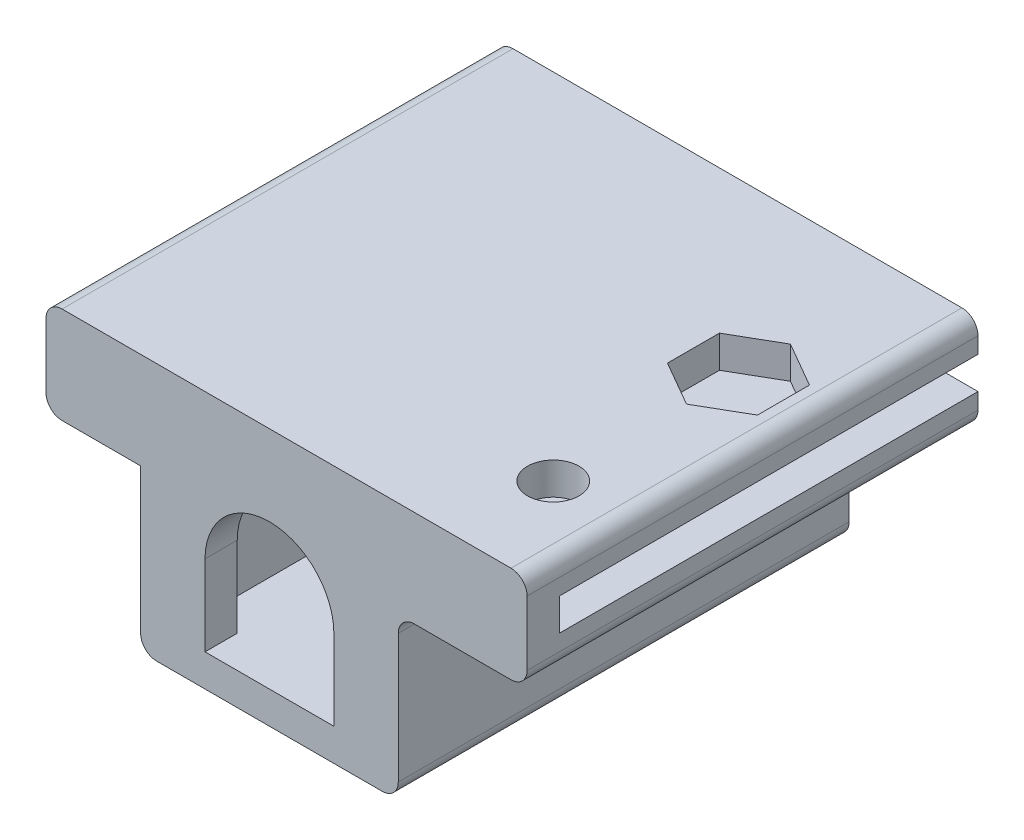
SolidWorks part; units mm, degrees
ref_plane "前视基准面" through (0, 0, 0) normal (0, 0, 1) x (1, 0, 0)
ref_plane "上视基准面" through (0, 0, 0) normal (0, 1, 0) x (1, 0, 0)
ref_plane "右视基准面" through (0, 0, 0) normal (1, 0, 0) x (0, 0, -1)
sketch "草图1" plane through (0, 0, 0) normal (0, 0, 1) x (1, 0, 0)
  line L0 (9, 3) -> (15, 3)
  line L1 (7, -7) -> (-7, -7)
  line L2 (8, -6) -> (8, 2)
  line L3 (8, 5) -> (-8, 5)
  line L4 (6, -4) -> (6, 4)
  line L5 (5, 5) -> (-5, 5)
  line L6 (-6, 4) -> (-6, -4)
  line L7 (-5, -5) -> (5, -5)
  line L8 (6, -4) -> (6, 4)
  line L9 (5, 5) -> (-5, 5)
  line L10 (-6, 4) -> (-6, -4)
  line L11 (-5, -5) -> (5, -5)
  line L12 (88.125, 7) -> (-11.875, 7)
  line L13 (-11.875, 7) -> (-11.875, 5)
  line L14 (-11.875, 5) -> (88.125, 5)
  line L15 (88.125, 5) -> (88.125, 7)
  line L16 (88.125, 7) -> (-11.875, 7)
  line L17 (-11.875, 7) -> (-11.875, 5)
  line L18 (-11.875, 5) -> (88.125, 5)
  line L19 (88.125, 5) -> (88.125, 7)
  line L20 (-8, -6) -> (-8, 3)
  line L21 (-12.875, 3) -> (-8, 3)
  line L22 (-13.875, 4) -> (-13.875, 8)
  line L23 (-12.875, 9) -> (15, 9)
  line L24 (16, 4) -> (16, 8)
  line L26 (4, 0) -> (4, -5)
  line L27 (4, -5) -> (-4, -5)
  line L28 (-4, 0) -> (-4, -5)
  arc A0 (4, 0) -> (-4, 0) centre (0, 0) ccw
  arc A1 (15, 9) -> (16, 8) centre (15, 8) cw
  arc A2 (8, 2) -> (9, 3) centre (9, 2) cw
  arc A3 (16, 4) -> (15, 3) centre (15, 4) cw
  arc A4 (6, 4) -> (5, 5) centre (5, 4) ccw
  arc A5 (-5, 5) -> (-6, 4) centre (-5, 4) ccw
  arc A6 (-6, -4) -> (-5, -5) centre (-5, -4) ccw
  arc A7 (5, -5) -> (6, -4) centre (5, -4) ccw
  arc A8 (6, 4) -> (5, 5) centre (5, 4) ccw
  arc A9 (-5, 5) -> (-6, 4) centre (-5, 4) ccw
  arc A10 (-6, -4) -> (-5, -5) centre (-5, -4) ccw
  arc A11 (5, -5) -> (6, -4) centre (5, -4) ccw
  arc A12 (8, -6) -> (7, -7) centre (7, -6) cw
  arc A13 (-7, -7) -> (-8, -6) centre (-7, -6) cw
  arc A14 (-13.875, 8) -> (-12.875, 9) centre (-12.875, 8) cw
  arc A15 (-12.875, 3) -> (-13.875, 4) centre (-12.875, 4) cw
  dimension "D3" = 1
  dimension "D5" = 2
  dimension "D6" = 2
  dimension "D1" = 0
  dimension "D2" = 0
extrude "凸台-拉伸1" add sketch "草图1" along normal blind 2 contours A11 L11 A10 L10 A9 L3 L18 L17 L16 L24 L23 L22 L21 L20 L1 L2 L0 A8 L8 | L18 L24 L16 L17 L3 | L11 A11 L8 A8 L3 A9 L10 A10 L28 A0 L26
sketch "草图2" plane through (0, 0, 0) normal (0, 0, -1) x (-1, 0, 0)
  line L1 (6, -5) -> (-6, -5)
  line L2 (6, -5) -> (6, 5)
  line L3 (6, 5) -> (-6, 5)
  line L4 (-6, 4) -> (-6, -4)
  line L5 (5, 5) -> (-5, 5)
  line L6 (6, -4) -> (6, 4)
  line L7 (-5, -5) -> (5, -5)
  line L8 (-6, 4) -> (-6, -4)
  line L9 (5, 5) -> (-5, 5)
  line L10 (6, -4) -> (6, 4)
  line L11 (-5, -5) -> (5, -5)
  line L12 (-16, 8) -> (-16, 4)
  line L13 (-15, 3) -> (-9, 3)
  line L14 (-8, 2) -> (-8, -6)
  line L15 (-7, -7) -> (7, -7)
  line L16 (8, -6) -> (8, 3)
  line L17 (8, 3) -> (12.875, 3)
  line L18 (13.875, 4) -> (13.875, 8)
  line L19 (12.875, 9) -> (-15, 9)
  line L23 (11.875, 7) -> (-88.125, 7)
  line L24 (-16, 8) -> (-16, 4)
  line L25 (-15, 3) -> (-9, 3)
  line L26 (-8, 2) -> (-8, -6)
  line L27 (-7, -7) -> (7, -7)
  line L28 (8, -6) -> (8, 3)
  line L29 (8, 3) -> (12.875, 3)
  line L30 (13.875, 4) -> (13.875, 8)
  line L31 (12.875, 9) -> (-15, 9)
  line L36 (-6, -5) -> (-6, 5)
  line L37 (11.875, 5) -> (11.875, 7)
  line L38 (-88.125, 5) -> (11.875, 5)
  line L39 (-88.125, 7) -> (-88.125, 5)
  line L40 (11.875, 7) -> (-88.125, 7)
  line L41 (11.875, 5) -> (11.875, 7)
  line L42 (-88.125, 5) -> (11.875, 5)
  line L43 (-88.125, 7) -> (-88.125, 5)
  arc A4 (-5, 5) -> (-6, 4) centre (-5, 4) ccw
  arc A5 (6, 4) -> (5, 5) centre (5, 4) ccw
  arc A6 (5, -5) -> (6, -4) centre (5, -4) ccw
  arc A7 (-6, -4) -> (-5, -5) centre (-5, -4) ccw
  arc A8 (-5, 5) -> (-6, 4) centre (-5, 4) ccw
  arc A9 (6, 4) -> (5, 5) centre (5, 4) ccw
  arc A10 (5, -5) -> (6, -4) centre (5, -4) ccw
  arc A11 (-6, -4) -> (-5, -5) centre (-5, -4) ccw
  arc A15 (-16, 4) -> (-15, 3) centre (-15, 4) ccw
  arc A16 (-16, 4) -> (-15, 3) centre (-15, 4) ccw
  arc A17 (-8, 2) -> (-9, 3) centre (-9, 2) ccw
  arc A18 (-8, 2) -> (-9, 3) centre (-9, 2) ccw
  arc A19 (-8, -6) -> (-7, -7) centre (-7, -6) ccw
  arc A20 (-8, -6) -> (-7, -7) centre (-7, -6) ccw
  arc A21 (7, -7) -> (8, -6) centre (7, -6) ccw
  arc A22 (7, -7) -> (8, -6) centre (7, -6) ccw
  arc A23 (12.875, 3) -> (13.875, 4) centre (12.875, 4) ccw
  arc A24 (12.875, 3) -> (13.875, 4) centre (12.875, 4) ccw
  arc A25 (13.875, 8) -> (12.875, 9) centre (12.875, 8) ccw
  arc A26 (13.875, 8) -> (12.875, 9) centre (12.875, 8) ccw
  arc A27 (-15, 9) -> (-16, 8) centre (-15, 8) ccw
  arc A28 (-15, 9) -> (-16, 8) centre (-15, 8) ccw
  dimension "D1" = 0
  dimension "D2" = 0
  dimension "D3" = 0
extrude "凸台-拉伸2" add sketch "草图2" along normal offset from surface (26 mm away) 2
sketch "草图3" plane through (0, 0, -26) normal (0, 0, -1) x (-1, 0, 0)
  line L1 (6, -5) -> (-6, -5)
  line L2 (6, -5) -> (6, -4)
  line L3 (6, -4) -> (-6, -4)
  line L4 (-6, -5) -> (-6, -4)
  line L20 (-16, 5) -> (-16, 4)
  line L21 (-15, 3) -> (-9, 3)
  line L22 (-8, 2) -> (-8, -6)
  line L23 (-7, -7) -> (7, -7)
  line L24 (8, -6) -> (8, 3)
  line L25 (8, 3) -> (12.875, 3)
  line L26 (13.875, 4) -> (13.875, 8)
  line L27 (12.875, 9) -> (-15, 9)
  line L28 (6, 5) -> (6, -5)
  line L29 (6, 5) -> (6, -5)
  line L30 (6, -5) -> (-6, -5)
  line L31 (6, -5) -> (-6, -5)
  line L37 (-15, 3) -> (-9, 3)
  line L38 (-8, 2) -> (-8, -6)
  line L39 (-7, -7) -> (7, -7)
  line L40 (8, -6) -> (8, 3)
  line L41 (8, 3) -> (12.875, 3)
  line L42 (13.875, 4) -> (13.875, 8)
  line L43 (12.875, 9) -> (-15, 9)
  line L48 (-6, -5) -> (-6, 5)
  line L49 (-6, -5) -> (-6, 5)
  line L50 (-6, 5) -> (-16, 5)
  line L51 (-6, 5) -> (-16, 5)
  line L52 (-16, 8) -> (-16, 7)
  line L53 (-16, 8) -> (-16, 7)
  line L54 (-16, 7) -> (11.875, 7)
  line L55 (-16, 7) -> (11.875, 7)
  line L56 (11.875, 7) -> (11.875, 5)
  line L57 (11.875, 7) -> (11.875, 5)
  line L58 (11.875, 5) -> (6, 5)
  line L59 (11.875, 5) -> (6, 5)
  line L60 (-16, 5) -> (-16, 4)
  arc A7 (-16, 4) -> (-15, 3) centre (-15, 4) ccw
  arc A8 (-16, 4) -> (-15, 3) centre (-15, 4) ccw
  arc A9 (-8, 2) -> (-9, 3) centre (-9, 2) ccw
  arc A10 (-8, 2) -> (-9, 3) centre (-9, 2) ccw
  arc A11 (-8, -6) -> (-7, -7) centre (-7, -6) ccw
  arc A12 (-8, -6) -> (-7, -7) centre (-7, -6) ccw
  arc A13 (7, -7) -> (8, -6) centre (7, -6) ccw
  arc A14 (7, -7) -> (8, -6) centre (7, -6) ccw
  arc A15 (12.875, 3) -> (13.875, 4) centre (12.875, 4) ccw
  arc A16 (12.875, 3) -> (13.875, 4) centre (12.875, 4) ccw
  arc A17 (13.875, 8) -> (12.875, 9) centre (12.875, 8) ccw
  arc A18 (13.875, 8) -> (12.875, 9) centre (12.875, 8) ccw
  arc A19 (-15, 9) -> (-16, 8) centre (-15, 8) ccw
  arc A20 (-15, 9) -> (-16, 8) centre (-15, 8) ccw
  line M19 (6, 5) -> (6, -5)
  line M20 (6, -5) -> (-6, -5)
  line M21 (-6, -5) -> (-6, 5)
  dimension "D2" = 1
  dimension "D1" = 0
extrude "凸台-拉伸3" add sketch "草图3" against normal blind 1.6 contours L3 M19 M21 M20
sketch "草图4" plane through (0, 9, 0) normal (0, 1, 0) x (1, 0, 0)
  line L0 (13.92, 16.825) -> (9.33, 14.175) construction
  line L2 (11.625, 12.2726) -> (14.42, 13.8863)
  line L3 (14.42, 13.8863) -> (14.42, 17.1137)
  line L4 (15, -2) -> (15, 26)
  line L5 (15, 26) -> (-12.875, 26)
  line L6 (15, -2) -> (15, 26)
  line L7 (-12.875, -2) -> (15, -2)
  line L9 (15, 26) -> (-12.875, 26)
  line L11 (-12.875, -2) -> (15, -2)
  line L12 (14.42, 17.1137) -> (11.625, 18.7274)
  line L13 (11.625, 18.7274) -> (8.83, 17.1137)
  line L14 (11.625, 18.15) -> (9.33, 16.825)
  line L15 (9.33, 16.825) -> (9.33, 14.175)
  line L16 (9.33, 14.175) -> (11.625, 12.85)
  line L17 (11.625, 12.85) -> (13.92, 14.175)
  line L18 (13.92, 14.175) -> (13.92, 16.825)
  line L19 (13.92, 16.825) -> (11.625, 18.15)
  line L20 (11.625, 18.15) -> (9.33, 16.825)
  line L21 (9.33, 16.825) -> (9.33, 14.175)
  line L22 (9.33, 14.175) -> (11.625, 12.85)
  line L23 (11.625, 12.85) -> (13.92, 14.175)
  line L24 (13.92, 14.175) -> (13.92, 16.825)
  line L25 (13.92, 16.825) -> (11.625, 18.15)
  line L26 (8.83, 17.1137) -> (8.83, 13.8863)
  line L27 (8.83, 13.8863) -> (11.625, 12.2726)
  line L31 (-12.875, 26) -> (-12.875, -2)
  line L32 (-12.875, 26) -> (-12.875, -2)
  circle A0 centre (11.625, 15.5) radius 2.795 construction
  dimension "D3" = 0.5
  dimension "D1" = 0
  dimension "D2" = 0
extrude "切除-拉伸1" cut sketch "草图4" against normal blind 2 contours L2 L3 L12 L13 L26 L27
sketch "草图5" plane through (0, 3, 0) normal (0, -1, 0) x (1, 0, 0)
  line L0 (11.625, -18.6754) -> (11.625, 2) construction
  line L1 (11.625, -18.6754) -> (14.375, -17.0877)
  line L2 (14.375, -17.0877) -> (14.375, -13.9123)
  line L3 (14.375, -13.9123) -> (11.625, -12.3246)
  line L4 (9, 2) -> (9, -26)
  line L5 (9, -26) -> (15, -26)
  line L6 (9, 2) -> (9, -26)
  line L7 (15, 2) -> (9, 2)
  line L9 (9, -26) -> (15, -26)
  line L11 (15, 2) -> (9, 2)
  line L12 (11.625, -12.3246) -> (8.875, -13.9123)
  line L13 (8.875, -13.9123) -> (8.875, -17.0877)
  line L14 (8.875, -17.0877) -> (11.625, -18.6754)
  line L19 (15, -26) -> (15, 2)
  line L20 (15, -26) -> (15, 2)
  circle A0 centre (11.625, -15.5) radius 1.25 construction
  circle A1 centre (11.625, -15.5) radius 1.25
  circle A2 centre (11.625, -15.5) radius 2.75 construction
  dimension "D2" = 5.5
  dimension "D1" = 0
extrude "切除-拉伸2" cut sketch "草图5" against normal blind 0.5 and the other way through all contours L12 L13 L14 L1 L2 L3
sketch "草图6" plane through (0, 3, 0) normal (0, -1, 0) x (1, 0, 0)
  line L0 (11.625, -18.6754) -> (11.625, 2) construction
  line L1 (14.375, -17.0877) -> (8.875, -13.9123) construction
  line L2 (8.625, -5.7321) -> (11.625, -7.4641)
  line L3 (11.625, -7.4641) -> (14.625, -5.7321)
  line L4 (14.375, -17.0877) -> (11.625, -18.6754)
  line L5 (9, -26) -> (15, -26)
  line L6 (14.375, -17.0877) -> (11.625, -18.6754)
  line L7 (15, 2) -> (9, 2)
  line L9 (9, -26) -> (15, -26)
  line L11 (15, 2) -> (9, 2)
  line L12 (14.625, -5.7321) -> (14.625, -2.2679)
  line L13 (14.625, -2.2679) -> (11.625, -0.5359)
  line L14 (14.375, -13.9123) -> (11.625, -12.3246)
  line L15 (11.625, -12.3246) -> (8.875, -13.9123)
  line L16 (8.875, -13.9123) -> (8.875, -17.0877)
  line L17 (8.875, -17.0877) -> (11.625, -18.6754)
  line L18 (11.625, -18.6754) -> (14.375, -17.0877)
  line L19 (14.375, -17.0877) -> (14.375, -13.9123)
  line L20 (14.375, -13.9123) -> (11.625, -12.3246)
  line L21 (11.625, -12.3246) -> (8.875, -13.9123)
  line L22 (8.875, -13.9123) -> (8.875, -17.0877)
  line L23 (8.875, -17.0877) -> (11.625, -18.6754)
  line L24 (11.625, -18.6754) -> (14.375, -17.0877)
  line L25 (14.375, -17.0877) -> (14.375, -13.9123)
  line L26 (11.625, -0.5359) -> (8.625, -2.2679)
  line L27 (8.625, -2.2679) -> (8.625, -5.7321)
  line L38 (11.625, -18.6754) -> (9, -17.1599)
  line L39 (11.625, -18.6754) -> (9, -17.1599)
  line L40 (9, -17.1599) -> (9, -26)
  line L41 (9, -17.1599) -> (9, -26)
  line L42 (15, -26) -> (15, 2)
  line L43 (15, -26) -> (15, 2)
  line L44 (9, 2) -> (9, -13.8401)
  line L45 (9, 2) -> (9, -13.8401)
  line L46 (9, -13.8401) -> (11.625, -12.3246)
  line L47 (9, -13.8401) -> (11.625, -12.3246)
  line L48 (11.625, -12.3246) -> (14.375, -13.9123)
  line L49 (11.625, -12.3246) -> (14.375, -13.9123)
  line L50 (14.375, -13.9123) -> (14.375, -17.0877)
  line L51 (14.375, -13.9123) -> (14.375, -17.0877)
  circle A0 centre (11.625, -4) radius 3 construction
  point P6 (11.625, -15.5)
  dimension "D3" = 6
  dimension "D4" = 11.5
  dimension "D1" = 0
  dimension "D2" = 0
extrude "切除-拉伸3" cut sketch "草图6" against normal blind 1 and the other way through all contours L2 L3 L12 L13 L26 L27
sketch "草图7" plane through (0, 4, 0) normal (0, -1, 0) x (1, 0, 0)
  line L0 (8.625, -2.2679) -> (8.625, -5.7321) construction
  line L1 (8.625, -5.7321) -> (11.625, -7.4641) construction
  line L2 (11.625, -7.4641) -> (14.625, -5.7321) construction
  line L3 (14.625, -5.7321) -> (14.625, -2.2679) construction
  line L4 (14.625, -2.2679) -> (11.625, -0.5359) construction
  line L5 (11.625, -0.5359) -> (8.625, -2.2679) construction
  line L6 (14.375, -13.9123) -> (11.625, -12.3246) construction
  line L7 (11.625, -12.3246) -> (8.875, -13.9123) construction
  line L8 (8.875, -13.9123) -> (8.875, -17.0877) construction
  line L9 (8.875, -17.0877) -> (11.625, -18.6754) construction
  line L10 (11.625, -18.6754) -> (14.375, -17.0877) construction
  line L11 (14.375, -17.0877) -> (14.375, -13.9123) construction
  line L12 (8.625, -2.2679) -> (8.625, -5.7321)
  line L13 (8.625, -5.7321) -> (11.625, -7.4641)
  line L14 (11.625, -7.4641) -> (14.625, -5.7321)
  line L15 (14.625, -5.7321) -> (14.625, -2.2679)
  line L16 (14.625, -2.2679) -> (11.625, -0.5359)
  line L17 (11.625, -0.5359) -> (8.625, -2.2679)
  line L18 (14.375, -13.9123) -> (11.625, -12.3246)
  line L19 (11.625, -12.3246) -> (8.875, -13.9123)
  line L20 (8.875, -13.9123) -> (8.875, -17.0877)
  line L21 (8.875, -17.0877) -> (11.625, -18.6754)
  line L22 (11.625, -18.6754) -> (14.375, -17.0877)
  line L23 (14.375, -17.0877) -> (14.375, -13.9123)
  line L24 (11.625, -7.4641) -> (11.625, -0.5359) construction
  circle A0 centre (11.625, -15.5) radius 1.35
  circle A1 centre (11.625, -4) radius 1.6
  dimension "D1" = 3.2
  dimension "D2" = 2.7
extrude "切除-拉伸4" cut sketch "草图7" against normal through all and the other way blind 1 contours A0 | A1
